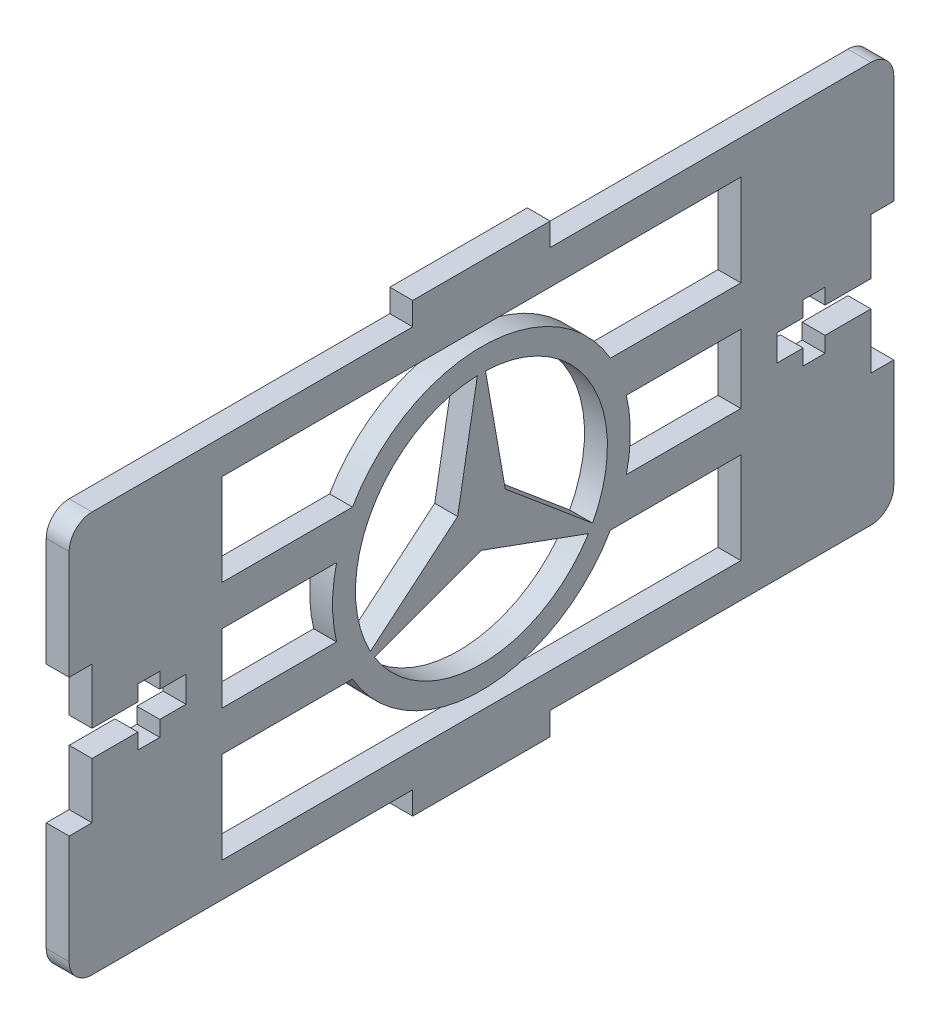
SolidWorks part; units mm, degrees
ref_plane "Front Plane" through (0, 0, 0) normal (0, 0, 1) x (1, 0, 0)
ref_plane "Top Plane" through (0, 0, 0) normal (0, 1, 0) x (1, 0, 0)
ref_plane "Right Plane" through (0, 0, 0) normal (1, 0, 0) x (0, 0, -1)
sketch "Sketch2" plane through (0, 0, 0) normal (1, 0, 0) x (0, 0, -1)
  line L0 (-45.72, 22.225) -> (-45.72, 7.62)
  line L1 (-45.72, 22.225) -> (45.72, 22.225) construction
  line L2 (-45.72, 22.225) -> (-45.72, -22.225) construction
  line L3 (-45.72, -22.225) -> (45.72, -22.225) construction
  line L4 (45.72, 22.225) -> (45.72, -22.225) construction
  line L5 (-45.72, 22.225) -> (45.72, -22.225) construction
  line L6 (-45.72, -22.225) -> (45.72, 22.225) construction
  line L7 (-45.72, 7.62) -> (-43.18, 7.62)
  line L8 (-43.18, 7.62) -> (-43.18, -7.62) construction
  line L9 (-43.18, -7.62) -> (-45.72, -7.62)
  line L10 (-45.72, -7.62) -> (-45.72, -22.225)
  line L11 (0, 22.225) -> (0, -22.225) construction
  line L12 (-45.72, 0) -> (45.72, 0) construction
  line L13 (43.18, -7.62) -> (45.72, -7.62)
  line L14 (43.18, 7.62) -> (43.18, -7.62) construction
  line L15 (45.72, 7.62) -> (43.18, 7.62)
  line L16 (-45.72, -22.225) -> (-7.62, -22.225)
  line L17 (-7.62, -22.225) -> (-7.62, -24.765)
  line L18 (-7.62, -24.765) -> (7.62, -24.765)
  line L19 (7.62, -24.765) -> (7.62, -22.225)
  line L20 (7.62, -22.225) -> (45.72, -22.225)
  line L21 (45.72, -22.225) -> (45.72, -7.62)
  line L22 (45.72, 7.62) -> (45.72, 22.225)
  line L23 (7.62, 24.765) -> (7.62, 22.225)
  line L24 (-7.62, 24.765) -> (7.62, 24.765)
  line L25 (-7.62, 22.225) -> (-7.62, 24.765)
  line L26 (45.72, 22.225) -> (7.62, 22.225)
  line L27 (-7.62, 22.225) -> (-45.72, 22.225)
  line L28 (-43.18, 7.62) -> (-43.18, 1.4478)
  line L29 (-43.18, 1.4478) -> (-38.1, 1.4478)
  line L30 (-38.1, 1.4478) -> (-38.1, 3.175)
  line L31 (-38.1, 3.175) -> (-35.6679, 3.175)
  line L32 (-35.6679, 3.175) -> (-35.6679, 1.4478)
  line L33 (-35.6679, 1.4478) -> (-32.766, 1.4478)
  line L34 (-32.766, 1.4478) -> (-32.766, -1.4478)
  line L35 (-38.1, -3.175) -> (-35.6679, -3.175)
  line L36 (-35.6679, -1.4478) -> (-32.766, -1.4478)
  line L37 (-35.6679, -3.175) -> (-35.6679, -1.4478)
  line L38 (-38.1, -1.4478) -> (-38.1, -3.175)
  line L39 (-43.18, -1.4478) -> (-38.1, -1.4478)
  line L40 (-43.18, -7.62) -> (-43.18, -1.4478)
  line L41 (43.18, -7.62) -> (43.18, -1.4478)
  line L42 (43.18, -1.4478) -> (38.1, -1.4478)
  line L43 (38.1, -1.4478) -> (38.1, -3.175)
  line L44 (38.1, -3.175) -> (35.6679, -3.175)
  line L45 (35.6679, -3.175) -> (35.6679, -1.4478)
  line L46 (35.6679, -1.4478) -> (32.766, -1.4478)
  line L47 (32.766, 1.4478) -> (32.766, -1.4478)
  line L48 (35.6679, 1.4478) -> (32.766, 1.4478)
  line L49 (35.6679, 3.175) -> (35.6679, 1.4478)
  line L50 (38.1, 3.175) -> (35.6679, 3.175)
  line L51 (38.1, 1.4478) -> (38.1, 3.175)
  line L52 (43.18, 1.4478) -> (38.1, 1.4478)
  line L53 (43.18, 7.62) -> (43.18, 1.4478)
  point P0 (0, 0)
  point P36 (-32.766, 0)
  dimension "D1" = 91.44
  dimension "D2" = 44.45
  dimension "D3" = 15.24
  dimension "D4" = 2.54
  dimension "D5" = 15.24
  dimension "D6" = 2.54
  dimension "D7" = 12.954
  dimension "D8" = 5.08
  dimension "D9" = 2.432
  dimension "D10" = 6.35
  dimension "D11" = 2.8956
extrude "Boss-Extrude1" add sketch "Sketch2" along normal blind 2.54
fillet "Fillet1" radius 2.54 4 edges at (1.27, -22.225, 45.72) (1.27, -22.225, -45.72) (1.27, 22.225, -45.72) (1.27, 22.225, 45.72)
sketch "Sketch3" plane through (2.54, 0, 0) normal (1, 0, 0) x (0, 0, -1)
  line L0 (0, 16.51) -> (0, 0) construction
  line L1 (0, 0) -> (-14.2981, -8.255) construction
  line L2 (0, 0) -> (14.2981, -8.255) construction
  line L3 (0, 16.51) -> (2.6396, 1.524) construction
  line L4 (2.6396, 1.524) -> (14.2981, -8.255) construction
  line L5 (0, 0) -> (2.6396, 1.524) construction
  line L6 (14.2981, -8.255) -> (0, -3.048) construction
  line L7 (0, 0) -> (0, -3.048) construction
  line L8 (-14.2981, -8.255) -> (0, -3.048) construction
  line L9 (-2.6396, 1.524) -> (-14.2981, -8.255) construction
  line L10 (0, 16.51) -> (-2.6396, 1.524) construction
  line L11 (2.6396, 1.524) -> (12.3165, -6.5928)
  line L12 (2.6396, 1.524) -> (0.4487, 13.9628)
  line L13 (0, -3.048) -> (11.8678, -7.37)
  line L14 (0, -3.048) -> (-11.8678, -7.37)
  line L15 (-2.6396, 1.524) -> (-0.4487, 13.9628)
  line L16 (-2.6396, 1.524) -> (-12.3165, -6.5928)
  circle A1 centre (0, 0) radius 16.51 construction
  circle A2 centre (0, 0) radius 13.97 construction
  arc A3 (0.4487, 13.9628) -> (12.3165, -6.5928) centre (0, 0) cw
  arc A4 (-11.8678, -7.37) -> (11.8678, -7.37) centre (0, 0) ccw
  arc A5 (-12.3165, -6.5928) -> (-0.4487, 13.9628) centre (0, 0) cw
  dimension "D1" = 27.94
  dimension "D2" = 33.02
  dimension "D3" = 120
  dimension "D4" = 3.048
extrude "Cut-Extrude2" cut sketch "Sketch3" against normal up to next
sketch "Sketch4" plane through (2.54, 0, 0) normal (1, 0, 0) x (0, 0, -1)
  line L0 (-28.7644, 18.415) -> (28.7644, 18.415)
  line L1 (28.7644, 18.415) -> (28.7644, 8.255)
  line L2 (28.7644, 8.255) -> (14.2981, 8.255)
  line L3 (0, 0) -> (0, 16.51) construction
  line L4 (-28.7644, 18.415) -> (-28.7644, 8.255)
  line L5 (-28.7644, 8.255) -> (-14.2981, 8.255)
  line L6 (0, 0) -> (16.51, 0) construction
  line L7 (-28.7644, -18.415) -> (-28.7644, -8.255)
  line L8 (28.7644, -18.415) -> (28.7644, -8.255)
  line L9 (28.7644, -8.255) -> (14.2981, -8.255)
  line L10 (-28.7644, -8.255) -> (-14.2981, -8.255)
  line L11 (-28.7644, -18.415) -> (28.7644, -18.415)
  line L12 (43.18, 22.225) -> (7.62, 22.225) construction
  line L13 (-16.0644, 3.81) -> (-28.7644, 3.81)
  line L14 (-28.7644, 3.81) -> (-28.7644, -3.81)
  line L15 (-28.7644, -3.81) -> (-16.0644, -3.81)
  line L16 (28.7644, -3.81) -> (16.0644, -3.81)
  line L17 (28.7644, 3.81) -> (28.7644, -3.81)
  line L18 (16.0644, 3.81) -> (28.7644, 3.81)
  circle A0 centre (0, 0) radius 16.51 construction
  arc A1 (-14.2981, 8.255) -> (14.2981, 8.255) centre (0, 0) cw
  arc A2 (-14.2981, -8.255) -> (14.2981, -8.255) centre (0, 0) ccw
  arc A3 (-16.0644, 3.81) -> (-16.0644, -3.81) centre (0, 0) ccw
  arc A4 (16.0644, 3.81) -> (16.0644, -3.81) centre (0, 0) cw
  dimension "D1" = 33.02
  dimension "D2" = 10.16
  dimension "D4" = 3.81
  dimension "D5" = 12.7
  dimension "D6" = 7.62
extrude "Cut-Extrude3" cut sketch "Sketch4" against normal blind 2.54
